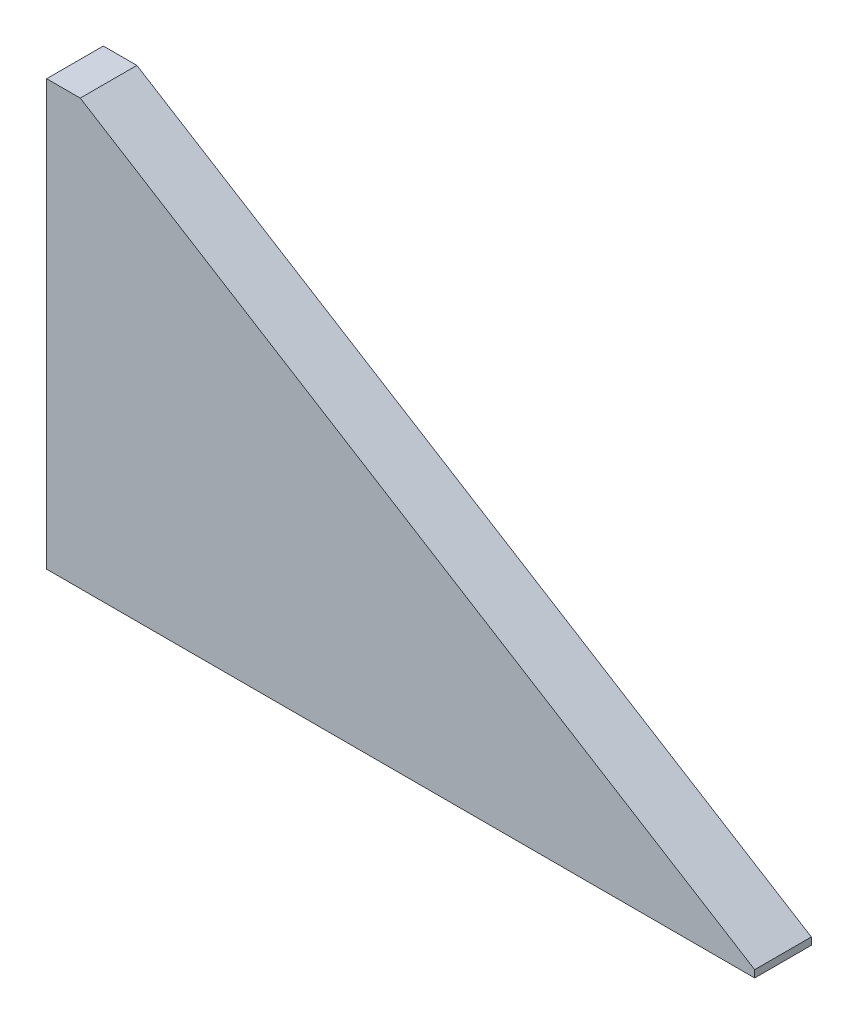
SolidWorks part; units mm, degrees
material "Acier galvanisé"
ref_plane "Plan de face" through (0, 0, 0) normal (0, 0, 1) x (1, 0, 0)
ref_plane "Plan de dessus" through (0, 0, 0) normal (0, 1, 0) x (1, 0, 0)
ref_plane "Plan de droite" through (0, 0, 0) normal (1, 0, 0) x (0, 0, -1)
sketch "Esquisse1" plane through (0, 0, 0) normal (1, 0, 0) x (0, 0, -1)
  line L1 (-4.8544, 59.1046) -> (3.1456, 59.1046)
  line L2 (-4.8544, 59.1046) -> (-4.8544, -0.8954)
  line L3 (-4.8544, -0.8954) -> (3.1456, -0.8954)
  line L4 (3.1456, 59.1046) -> (3.1456, -0.8954)
  dimension "D1" = 8
  dimension "D2" = 60
extrude "Boss.-Extru.1" add sketch "Esquisse1" against normal blind 100
sketch "Esquisse2" plane through (0, 0, 4.8544) normal (0, 0, 1) x (1, 0, 0)
  line L0 (-96, 59.5638) -> (1.0705, 60.732)
  line L1 (-96, 59.5638) -> (2.1843, -1.2249)
  line L2 (2.1843, -1.2249) -> (1.0705, 60.732)
  line L4 (-100, -0.8954) -> (-100, 59.1046) construction
  dimension "D1" = 4
extrude "Enlèv. mat.-Extru.1" cut sketch "Esquisse2" against normal up to next
